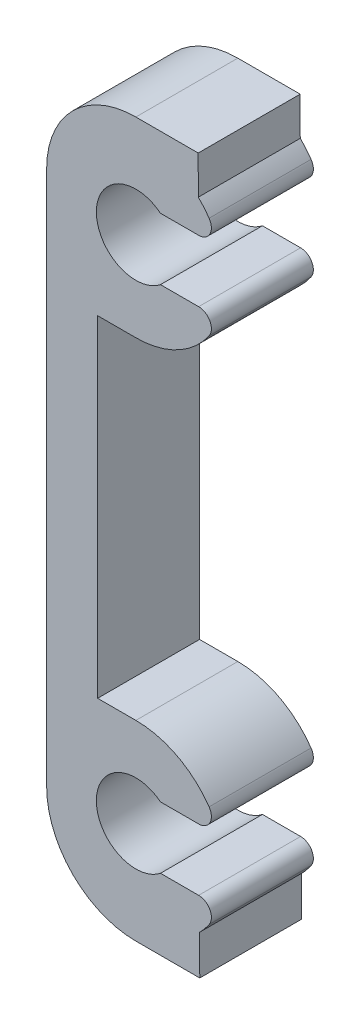
SolidWorks part; units mm, degrees
ref_plane "Front Plane" through (0, 0, 0) normal (0, 0, 1) x (1, 0, 0)
ref_plane "Top Plane" through (0, 0, 0) normal (0, 1, 0) x (1, 0, 0)
ref_plane "Right Plane" through (0, 0, 0) normal (1, 0, 0) x (0, 0, -1)
sketch "Sketch1" plane through (0, 0, 0) normal (0, 0, 1) x (1, 0, 0)
  line L3 (-7.2538, 14) -> (-7.5538, 14) construction
  line L4 (-10, 14) -> (-7.5538, 14)
  line L6 (-12.5, -10) -> (-12.5, 10) construction
  line L9 (-11.5, -6.5) -> (-11.5, 6.5)
  line L11 (-13.5, -10.5) -> (-13.5, 10.5)
  line L19 (-10, 6.5) -> (-11.5, 6.5)
  line L21 (-7.5505, 12.5) -> (-7.5538, 14)
  line L22 (-10, -14) -> (-7.4932, -14)
  line L23 (-10, 12.5) -> (-6.77, 12.5) construction
  line L32 (-16.0714, 0) -> (15.8107, 0) construction
  line L36 (-7.4966, -12.446) -> (-7.4932, -14)
  line L41 (-10, -6.5) -> (-11.5, -6.5)
  circle A0 centre (-10, 10) radius 3.5 construction
  arc A1 (-10, 6.5) -> (-7.5505, 12.5) centre (-10, 10) ccw
  arc A18 (-13.5, 10.5) -> (-10, 14) centre (-10, 10.5) cw
  arc A22 (-13.5, -10.5) -> (-10, -14) centre (-10, -10.5) ccw
  arc A23 (-10, -6.5) -> (-7.4966, -12.446) centre (-10, -10) cw
  point P1 (-12.5, 0)
  point P11 (0, 0)
  point P30 (-11.5, 0)
  dimension "D3" = 3.5
  dimension "D1" = 3.5
  dimension "D2" = 2
extrude "Boss-Extrude1" add sketch "Sketch1" along normal blind 4
sketch "Sketch2" plane through (0, 0, 0) normal (0, 0, 1) x (1, 0, 0)
  circle A0 centre (-10, -10) radius 1.55 construction
  circle A3 centre (-10, -10) radius 1.55
  circle A6 centre (-10, 10) radius 1.55 construction
  circle A7 centre (-10, 10) radius 1.55
extrude "Cut-Extrude4" cut sketch "Sketch2" along normal up to next
sketch "Sketch3" plane through (0, 0, 4) normal (0, 0, 1) x (1, 0, 0)
  line L0 (-9.0343, 11.2124) -> (-6.7167, 11.2124)
  line L1 (-9.0343, 8.7876) -> (-6.7167, 8.7876)
  circle A0 centre (-10, 10) radius 1.55 construction
  arc A1 (-10, 6.5) -> (-7.5505, 12.5) centre (-10, 10) ccw construction
  arc A2 (-9.0343, 8.7876) -> (-9.0343, 11.2124) centre (-10, 10) ccw
  arc A3 (-6.7167, 8.7876) -> (-6.7167, 11.2124) centre (-10, 10) ccw
extrude "Cut-Extrude5" cut sketch "Sketch3" against normal through all
ref_plane "Plane1" through (0, 0, 0) normal (0, -1, 0) x (-1, 0, 0)
mirror "Mirror1" about plane through (0, 0, 0) normal (0, -1, 0) of "Cut-Extrude5"
fillet "Fillet1" radius 0.5 4 edges at (-6.7167, 8.7876, 2) (-6.7167, 11.2124, 2) (-6.7167, -11.2124, 2) (-6.7167, -8.7876, 2)
